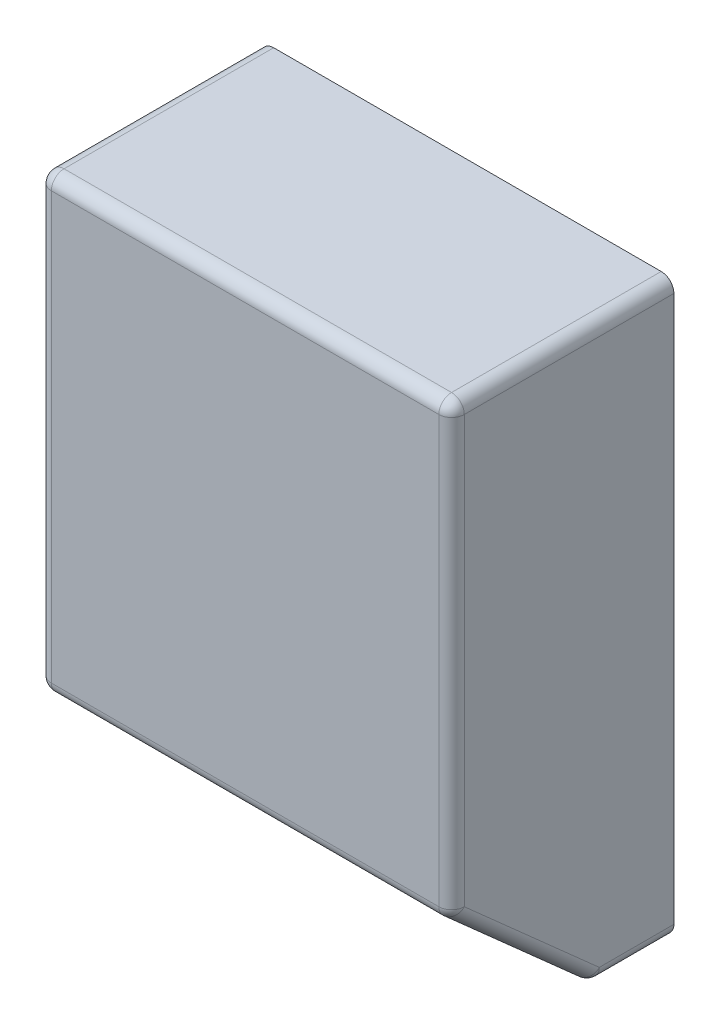
SolidWorks part; units mm, degrees
ref_plane "Front Plane" through (0, 0, 0) normal (0, 0, 1) x (1, 0, 0)
ref_plane "Top Plane" through (0, 0, 0) normal (0, 1, 0) x (1, 0, 0)
ref_plane "Right Plane" through (0, 0, 0) normal (1, 0, 0) x (0, 0, -1)
sketch "Sketch1" plane through (0, 0, 0) normal (0, 0, 1) x (1, 0, 0)
  line L1 (-65, 90) -> (65, 90)
  line L2 (-65, 90) -> (-65, -90)
  line L3 (-65, -90) -> (65, -90)
  line L4 (65, 90) -> (65, -90)
  line L5 (-65, 90) -> (65, -90) construction
  line L6 (-65, -90) -> (65, 90) construction
  point P0 (0, 0)
  dimension "D1" = 130
  dimension "D2" = 180
extrude "Boss-Extrude1" add sketch "Sketch1" along normal blind 70 contours L2 L3 L4 L1
sketch "Sketch2" plane through (-65, 0, 0) normal (-1, 0, 0) x (0, 0, 1)
  line L0 (70, -50) -> (25, -90)
  line L1 (70, 90) -> (70, -90) construction
  line L2 (70, -90) -> (0, -90) construction
  line L3 (25, -90) -> (70, -90)
  line L4 (70, -90) -> (70, -50)
  dimension "D1" = 25
  dimension "D2" = 40
extrude "Cut-Extrude1" cut sketch "Sketch2" against normal through all
fillet "Fillet2" radius 4 11 edges at (0, 90, 70) (-65, 90, 35) (65, 90, 35) (0, -90, 25) (65, -90, 12.5) (-65, -90, 12.5) (65, 20, 70) (65, -70, 47.5) (0, -50, 70) (-65, -70, 47.5) (-65, 20, 70)
shell "Shell1" thickness 2.5
sketch "Sketch3" plane through (0, -62.6897, 55.7241) normal (0, -0.7474, 0.6644) x (1, 0, 0)
  line L0 (-61, -39.5867) -> (61, -39.5867) construction
  line L1 (-61, 17.3042) -> (-61, -39.5867) construction
  line L4 (18.994, -32.0867) -> (18.994, 12.9133)
  line L5 (-41.006, -32.0867) -> (18.994, -32.0867)
  line L6 (-41.006, 12.9133) -> (-41.006, -32.0867)
  line L7 (-41.006, 12.9133) -> (18.994, 12.9133)
  circle A1 centre (40.0001, -9.5867) radius 8
  dimension "D1" = 16
  dimension "D5" = 30
  dimension "D2" = 60
  dimension "D3" = 45
  dimension "D4" = 7.5
  dimension "D6" = 19.994
extrude "Cut-Extrude2" cut sketch "Sketch3" against normal blind 10
sketch "Sketch4" plane through (0, -62.6897, 55.7241) normal (0, -0.7474, 0.6644) x (1, 0, 0)
  line L0 (-61, -39.5867) -> (61, -39.5867) construction
  line L4 (25.794, 15.4133) -> (-43.506, 15.4133)
  line L5 (-43.506, 15.4133) -> (-43.506, -34.5867)
  line L6 (-43.506, -34.5867) -> (25.794, -34.5867)
  line L7 (25.794, -34.5867) -> (25.794, 15.4133)
  dimension "D1" = 50
  dimension "D2" = 69.3
  dimension "D3" = 5
extrude "Cut-Extrude3" cut sketch "Sketch4" along normal blind 1 from surface at -2.5 starting at face at (40.0001, -61.8753, 52.8773)
